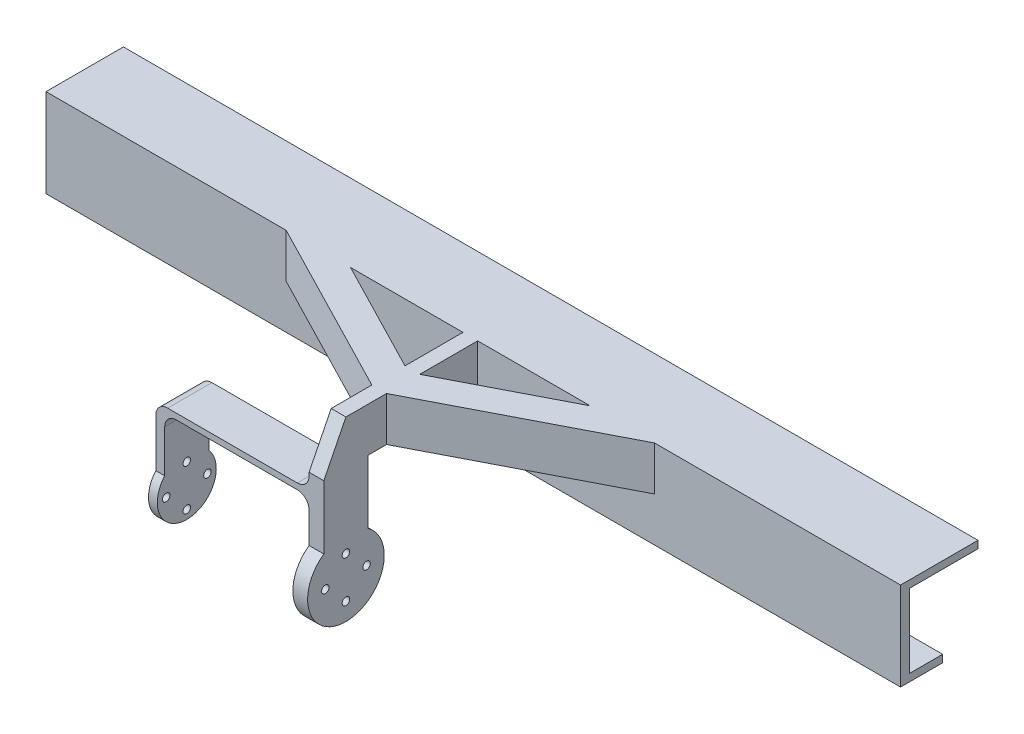
SolidWorks part; units mm, degrees
ref_plane "Front Plane" through (0, 0, 0) normal (0, 0, 1) x (1, 0, 0)
ref_plane "Top Plane" through (0, 0, 0) normal (0, 1, 0) x (1, 0, 0)
ref_plane "Right Plane" through (0, 0, 0) normal (1, 0, 0) x (0, 0, -1)
ref_plane "Plane1" through (0, 0, 1.7155) normal (0, 0, 1) x (1, 0, 0)
sketch "Sketch2" plane through (0, 0, 1.7155) normal (0, 0, 1) x (1, 0, 0)
  line L0 (145, 0) -> (-145, 0) construction
  line L1 (145, 15) -> (-145, 15)
  line L3 (145, -15) -> (-145, -15)
  line L5 (140, 12.5) -> (-140, 12.5)
  line L7 (140, -12.5) -> (-140, -12.5)
  line L12 (145, 15) -> (145, -15)
  line L13 (-140, 12.5) -> (-140, -12.5)
  line L14 (-145, 15) -> (-145, -15)
  line L15 (140, 12.5) -> (140, -12.5)
  dimension "D1" = 25
  dimension "D2" = 30
  dimension "D3" = 5
  dimension "D4" = 290
  dimension "D6" = 5
extrude "Boss-Extrude1" add sketch "Sketch2" along normal blind 23.28
sketch "Sketch3" plane through (0, 0, 24.9955) normal (0, 0, 1) x (1, 0, 0)
  line L1 (145, 15) -> (-145, 15)
  line L2 (145, 15) -> (145, -15)
  line L3 (145, -15) -> (-145, -15)
  line L4 (-145, 15) -> (-145, -15)
extrude "Boss-Extrude2" add sketch "Sketch3" along normal blind 3
sketch "Sketch4" plane through (145, 0, 0) normal (1, 0, 0) x (0, 0, -1)
  line L0 (-27.9955, -15) -> (-27.9955, 15) construction
  line L1 (-1.7155, -12.5) -> (-24.9955, -12.5)
  line L2 (-1.7155, -12.5) -> (-1.7155, 12.5)
  line L3 (-1.7155, 12.5) -> (-24.9955, 12.5)
  line L4 (-24.9955, -12.5) -> (-24.9955, 12.5)
  line L5 (-27.9955, -15) -> (-1.7155, -15) construction
  line L7 (-1.7155, -15) -> (-1.7155, 15) construction
  line L10 (-24.9955, 12.5) -> (-1.7155, 12.5) construction
  dimension "D1" = 3
  dimension "D2" = 2.5
extrude "Cut-Extrude1" cut sketch "Sketch4" against normal through all and the other way through all
ref_plane "Plane3" through (-0.5, 0, 0) normal (-1, 0, 0) x (0, 0, 1)
sketch "Sketch5" plane through (-0.5, 0, 0) normal (1, 0, 0) x (0, 0, -1)
  line L4 (-27.9955, 0) -> (-27.9955, 15)
  line L5 (-27.9955, 15) -> (-72.7155, 15)
  line L6 (-65.2155, 0) -> (-65.2155, -21.5316)
  line L7 (-27.9955, 0) -> (-65.2155, 0)
  line L8 (-80.2155, 0) -> (-80.2155, -21.5316)
  line L9 (-80.2155, 0) -> (-72.7155, 15)
  line L10 (-27.9955, -15) -> (-27.9955, 15) construction
  line L11 (-27.9955, 15) -> (-1.7155, 15) construction
  arc A0 (-80.2155, -21.5316) -> (-65.2155, -21.5316) centre (-72.7155, -32.15) ccw
  dimension "D3" = 13
  dimension "D4" = 52.22
  dimension "D1" = 15
  dimension "D2" = 15
  dimension "D5" = 47.15
  dimension "D6" = 13.4164
extrude "Boss-Extrude3" add sketch "Sketch5" along normal blind 2 and the other way blind 3
sketch "Sketch6" plane through (-3.5, 0, 0) normal (1, 0, 0) x (0, 0, -1)
  circle A0 centre (-72.7155, -32.15) radius 10
  arc A1 (-80.2155, -21.5316) -> (-65.2155, -21.5316) centre (-72.7155, -32.15) ccw construction
  dimension "D1" = 20
extrude "Cut-Extrude2" cut sketch "Sketch6" along normal blind 2
sketch "Sketch7" plane through (-3.5, 0, 0) normal (-1, 0, 0) x (0, 0, 1)
  line L0 (72.7155, -27.3874) -> (72.7155, -79.0243) construction
  line L1 (65.2155, -21.5316) -> (65.2155, 0) construction
  line L6 (80.2155, 0) -> (80.2155, -21.5316) construction
  line L7 (-104.8443, -32.15) -> (-53.4231, -32.15) construction
  circle A0 centre (72.7155, -25.15) radius 1.275
  circle A1 centre (79.7155, -32.15) radius 1.275
  circle A2 centre (72.7155, -39.15) radius 1.275
  circle A3 centre (65.7155, -32.15) radius 1.275
  arc A5 (65.2155, -21.5316) -> (80.2155, -21.5316) centre (72.7155, -32.15) ccw construction
  point P32 (72.7155, -32.15)
  dimension "D1" = 2.55
  dimension "D5" = 2.55
  dimension "D6" = 2.55
  dimension "D7" = 2.55
  dimension "D2" = 7
  dimension "D3" = 7
  dimension "D4" = 7
  dimension "D8" = 7
extrude "Cut-Extrude3" cut sketch "Sketch7" against normal blind 10
sketch "Sketch8" plane through (0, 0, 1.7155) normal (0, 0, -1) x (-1, 0, 0)
  line L1 (-145, -15) -> (145, -15)
  line L2 (-145, -15) -> (-145, -12.5)
  line L3 (-145, -12.5) -> (145, -12.5)
  line L4 (145, -15) -> (145, -12.5)
extrude "Cut-Extrude4" cut sketch "Sketch8" against normal blind 12
sketch "Sketch9" plane through (0, 15, 0) normal (0, 1, 0) x (1, 0, 0)
  line L0 (-3.5, -58.9222) -> (-63.5, -27.9955)
  line L3 (-3.5, -47.672) -> (-41.6737, -27.9955)
  line L4 (-3.5, -27.9955) -> (-3.5, -72.7155) construction
  line L5 (-3.5, -58.9222) -> (-3.5, -47.672)
  line L6 (-3.5, -27.9955) -> (-145, -27.9955) construction
  line L7 (-63.5, -27.9955) -> (-41.6737, -27.9955)
  line L8 (-1, -64.4544) -> (-1, -20.3652) construction
  line L9 (1.5, -27.9955) -> (1.5, -72.7155) construction
  line L10 (61.5, -27.9955) -> (39.6737, -27.9955)
  line L11 (1.5, -58.9222) -> (1.5, -47.672)
  line L12 (1.5, -47.672) -> (39.6737, -27.9955)
  line L13 (1.5, -58.9222) -> (61.5, -27.9955)
  dimension "D1" = 60
  dimension "D2" = 10
extrude "Boss-Extrude4" add sketch "Sketch9" against normal up to surface (15 mm away) up to face at (-1, 0, 46.6055)
sketch "Esquisse1" plane through (-3.5, 0, 0) normal (-1, 0, 0) x (0, 0, 1)
  line L1 (65.2155, -7.15) -> (80.2155, -7.15)
  line L2 (65.2155, -7.15) -> (65.2155, -5.15)
  line L3 (65.2155, -5.15) -> (80.2155, -5.15)
  line L4 (80.2155, -7.15) -> (80.2155, -5.15)
  circle A0 centre (72.7155, -32.15) radius 10 construction
  dimension "D1" = 2
  dimension "D2" = 25
extrude "Boss.-Extru.1" add sketch "Esquisse1" along normal blind 49
sketch "Esquisse2" plane through (-52.5, 0, 0) normal (-1, 0, 0) x (0, 0, 1)
  line L4 (65.2155, -21.5316) -> (65.2155, -25.5356)
  line L5 (80.2155, -21.5316) -> (80.2155, -25.5356)
  line L6 (65.2155, -7.15) -> (65.2155, -12.8284)
  line L9 (65.2155, -7.15) -> (65.2155, -5.15)
  line L10 (65.2155, -5.15) -> (80.2155, -5.15)
  line L11 (80.2155, -5.15) -> (80.2155, -7.15)
  line L12 (65.2155, -12.8284) -> (65.2155, -21.5316)
  line L13 (80.2155, -7.15) -> (80.2155, -21.5316)
  circle A0 centre (72.7155, -39.15) radius 1.275 construction
  circle A1 centre (79.7155, -32.15) radius 1.275 construction
  circle A2 centre (72.7155, -25.15) radius 1.275 construction
  circle A3 centre (65.7155, -32.15) radius 1.275 construction
  circle A4 centre (72.7155, -32.15) radius 10 construction
  circle A5 centre (72.7155, -39.15) radius 1.275
  circle A6 centre (79.7155, -32.15) radius 1.275
  circle A7 centre (72.7155, -25.15) radius 1.275
  circle A8 centre (65.7155, -32.15) radius 1.275
  arc A9 (65.2155, -25.5356) -> (80.2155, -25.5356) centre (72.7155, -32.15) ccw
extrude "Boss.-Extru.2" add sketch "Esquisse2" along normal blind 3
fillet "Congé1" radius 4 4 edges at (-3.5, -5.15, 72.7155) (-3.5, -7.15, 72.7155) (-52.5, -7.15, 72.7155) (-55.5, -5.15, 72.7155)
